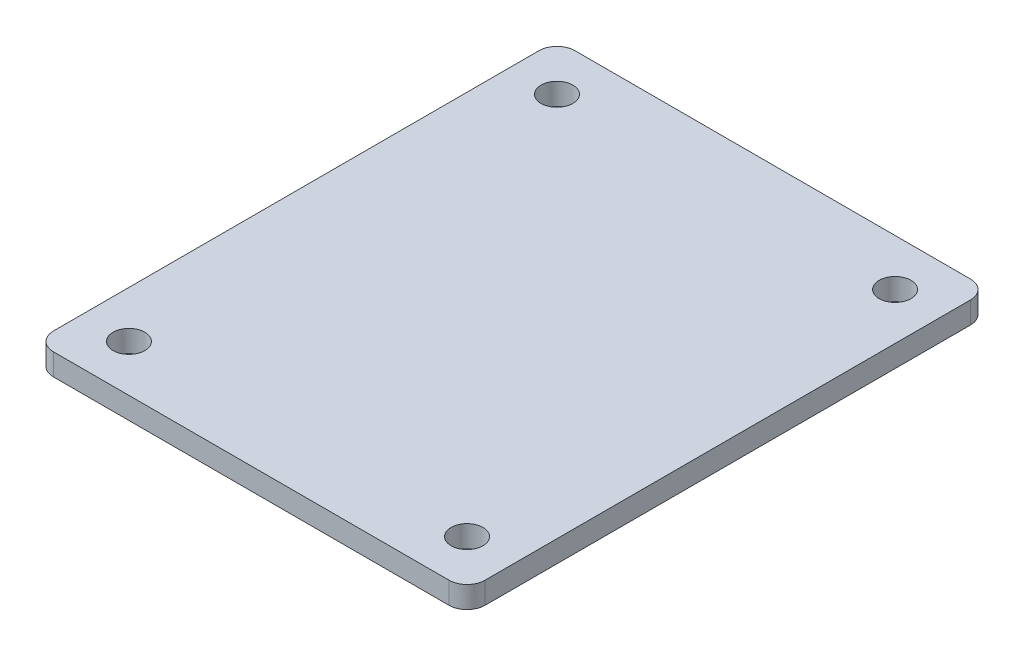
SolidWorks part; units mm, degrees
material "Acrylic (Medium-high impact)"
ref_plane "Front Plane" through (0, 0, 0) normal (0, 0, 1) x (1, 0, 0)
ref_plane "Top Plane" through (0, 0, 0) normal (0, 1, 0) x (1, 0, 0)
ref_plane "Right Plane" through (0, 0, 0) normal (1, 0, 0) x (0, 0, -1)
sketch "Sketch1" plane through (0, 0, 0) normal (0, 1, 0) x (1, 0, 0)
  line L1 (0, 0) -> (60.96, 0)
  line L2 (0, 0) -> (0, 73.66)
  line L3 (0, 73.66) -> (60.96, 73.66)
  line L4 (60.96, 0) -> (60.96, 73.66)
  dimension "D1" = 73.66
  dimension "D2" = 60.96
extrude "Boss-Extrude1" add sketch "Sketch1" along normal blind 3.0734
fillet "Fillet1" radius 2.54 4 edges at (60.96, 1.5367, -73.66) (0, 1.5367, -73.66) (60.96, 1.5367, 0) (0, 1.5367, 0)
hole_wizard "#8 Clearance Hole1" positions "Sketch2" profile "Sketch3" hole size "#8" standard "ANSI Inch" end condition through all
sketch "Sketch2" plane through (0, 3.0734, 0) normal (0, 1, 0) x (1, 0, 0)
  line L0 (60.96, 36.83) -> (0, 36.83) construction
  line L1 (60.96, 2.54) -> (60.96, 71.12) construction
  line L2 (0, 71.12) -> (0, 2.54) construction
  line L5 (30.48, 0) -> (30.48, 73.66) construction
  line L6 (2.54, 0) -> (58.42, 0) construction
  line L7 (58.42, 73.66) -> (2.54, 73.66) construction
  line L10 (54.356, 67.056) -> (6.604, 67.056) construction
  line L13 (54.356, 67.056) -> (54.356, 6.604) construction
  point P0 (54.356, 67.056)
  point P2 (54.356, 6.604)
  point P4 (6.604, 67.056)
  point P39 (54.356, 36.83)
  point P40 (30.48, 67.056)
  point P41 (6.604, 6.604)
  dimension "D1" = 47.752
  dimension "D2" = 60.452
sketch "Sketch3" plane through (54.356, 3.0734, -67.056) normal (1, 0, 0) x (0, 0, 1)
  line L0 (0, 0) -> (0, 3.0734)
  line L1 (0, 3.0734) -> (2.2479, 3.0734)
  line L2 (2.2479, 3.0734) -> (2.2479, 0)
  line L5 (2.2479, 0) -> (0, 0)
  line L11 (0, -6.35) -> (0, 107.95) construction
  dimension "Thru Hole Dia." = 4.4958
  dimension "Thru Hole Depth" = 3.0734
equation "\"Height\"= 32in"
equation "\"Width\"= 23in"
equation "\"Depth\"= 20in"
equation "\"Plexi\"= .121in"
equation "\"EBWidth\" = 9in"
equation "\"ComponentMountDia\"=0.1770"
equation "\"MagnetThickness\"= 0.125in"
equation "\"MagnetDiameter\"= 12mm"
equation "\"DoorPlexi\" = \"Plexi\""
equation "\"ShelfThickness\" = .1250in"
equation "\"BasePlateThickness\" = 0.5in"
equation "\"BasePlateWidth\" = \"Width\"+\"EBWidth\"-2*\"Plexi\""
equation "\"BasePlateDepth\" = \"TopBarDepth\"+2*\"CornerCube\""
equation "\"Boxsize\" = .75in"
equation "\"BoxsizeHalf\" = \"Boxsize\"/2"
equation "\"Boxinner\" = .625in"
equation "\"CornerCube\" = 0.75in"
equation "\"FingerLength\" = 1.125in"
equation "\"FingerWidth\" = .625in"
equation "\"Cutwidth\"= .016in"
equation "\"Earsize\"= 1in + \"Cutwidth\" /2"
equation "\"Slotsize\" = 1in - \"CutWidth\" / 2"
equation "\"InnerWidth\" = \"Width\" - 2* \"Plexi\""
equation "\"InnerHeight\" = \"Height\" -2 * \"Plexi\""
equation "\"InnerDepth\" = \"Depth\" - 2*\"Plexi\""
equation "\"FrontDoorGap\" = .1in"
equation "\"TopDepth\" = \"Depth\"-\"DoorPlexi\"-\"FrontDoorGap\""
equation "\"TopBarDepth\" = \"Depth\"-\"DoorPlexi\"-\"Plexi\"-2*\"MagnetThickness\"-2*\"CornerCube\""
equation "\"RearNumHoles\" = 4"
equation "\"RearHolesBorder\" = 2.25"
equation "\"RearHoleSpacing\" = (\"Width\" - 2*\"RearHolesBorder\") / (\"RearNumHoles\"-1)"
equation "\"RearBarLength\" = (\"InnerWidth\"-2*\"CornerCube\")"
equation "\"RearTopNumHoles\" = 4"
equation "\"RearTopHolesBorder\" = 3.1"
equation "\"RearTopHolesSpacing\" = (\"Width\" - 2*\"RearTopHolesBorder\") / (\"RearTopNumHoles\"-1)"
equation "\"SideTopNumHoles\" = 4"
equation "\"SideTopHoleOffset\"=\"CornerCube\"+\"FingerLength\"+\"Plexi\"+.5"
equation "\"SideTopHoleSpacing\" = (\"TopBarDepth\"-2*\"SideTopHoleOffset\") / (\"SideTopNumHoles\"-1)"
equation "\"SideHorizNumHoles\" = 4"
equation "\"SideHorizHoleBorder\" = 1.50"
equation "\"SideHorizHoleSpacing\" = (\"TopBarDepth\"-2*\"SideHorizHoleBorder\") / (\"SideHorizNumHoles\"-1)"
equation "\"SideVertBarLength\"=\"Height\"-\"BasePlateThickness\"-2*\"CornerCube\"-\"Plexi\""
equation "\"SideVertNumHoles\" = 4"
equation "\"SideVertHolesBorder\" = \"CornerCube\"+\"FingerLength\"+1.50"
equation "\"SideVertHoleSpacing\" = (\"SideVertBarLength\" - 2*(\"SideVertHolesBorder\"-\"Plexi\"-\"CornerCube\")) / (\"SideVertNumHoles\"-1)"
equation "\"RearSideVertNumHoles\" = 4"
equation "\"RearSideVertHolesBorder\" = 2.4"
equation "\"RearSideVertHoleSpacing\" = (\"SideVertBarLength\" - 2*(\"RearSideVertHolesBorder\"-\"Plexi\"-\"CornerCube\")) / (\"RearSideVertNumHoles\"-1)"
equation "\"Rivet3_16Dia\" = .191in"
equation "\"RivetDia\" = .228in"
equation "\"BinderPostDia\" = .228in"
equation "\"SlotDepth\" = \"Plexi\" + 0.75in + .005in"
equation "\"SideSlotWidth\"   = \"Plexi\"+.005in"
equation "\"SidePanelVertSpacing\" = (\"Height\"-2*(1.75-\"Plexi\")) / 5"
equation "\"BottomPanelSideHoleSpacing\" = (\"InnerDepth\"-2*(1.75-\"Plexi\")) / 4"
equation "\"CoolerDepth\" = 12in"
equation "\"ShelfGap\" = 0.5in"
equation "\"ShelfDepth\" = \"TopBarDepth\"+\"CornerCube\"-\"CoolerDepth\""
equation "\"ShelfBarDepth\"=\"ShelfDepth\"-2*\"CornerCube\""
equation "\"ShelfWidth\" = \"EBWidth\"-\"ShelfGap\""
equation "\"ShelfBarWidth\" = \"EBWidth\"-\"Boxsize\""
equation "\"ShelfBarWidthShort\" = \"ShelfBarWidth\"-\"Boxsize\"-\"ShelfGap\""
equation "\"ShelfHeight1\" = 13in"
equation "\"ShelfHeight2\" = 24in"
equation "\"IntakeWidth\"=4in"
equation "\"IntakeHeight\"=2in"
equation "\"ExhaustWidth\"=4in"
equation "\"ExhaustHeight\"=2in"
equation "\"VentSpacing\"=7in"
equation "\"VentVertLocation\"=12.75in"
equation "\"AngleBracketLengthShort\"=.625in"
equation "\"AngleBracketLengthLong\"=1in"
equation "\"AngleBracketWidth\"=.5in"
equation "\"AngleBracketThickness\"=.125in"
equation "\"AngleBracketHolePosShort\"=.358in"
equation "\"AngleBracketHolePosLong\"=.7in"
equation "\"AngleBracketHoleDia\"=\"Rivet3_16Dia\""
equation "\"ShelfBarAngleHole\"=\"ShelfGap\"+\"Boxsize\"+\"AngleBracketHolePosShort\""
equation "\"PSBracketThickness\" = .0641in"
equation "\"EBForwardMountOffset\" = 4.0in"
equation "\"EBForwardMount\" = 2*\"Boxsize\"+\"CoolerDepth\"+\"EBForwardMountOffset\""
equation "\"EBRearwardMountOffset\" = 1.5in"
equation "\"EBRearwardMount\"= \"Boxsize\"+\"EBRearwardMountOffset\""
equation "\"MagSealWidth\" = \"InnerWidth\""
equation "\"MagSealHeight\" = \"Height\"-\"BasePlateThickness\"-\"Plexi\""
equation "\"MagWidth\" = .500in"
equation "\"SiliconeSealOD\" = .3125in"
equation "\"SiliconeSealID\" = .1875in"
equation "\"SiliconeSealWidth\" = \"MagSealWidth\" - 2*\"MagWidth\"-\"SiliconeSealOD\""
equation "\"SiliconeSealHeigth\" = \"MagSealHeight\" - 2*\"MagWidth\"-\"SiliconeSealOD\""
equation "\"HooknLoopThick\" = .085in"
equation "\"HooknLoopWidth\" = 0.75in"
equation "\"HooknLoopHeigth\" = 0.75in"
equation "\"RivNutHeight\" = 0.015in"
equation "\"D1@Boss-Extrude1\"=\"Plexi\""
